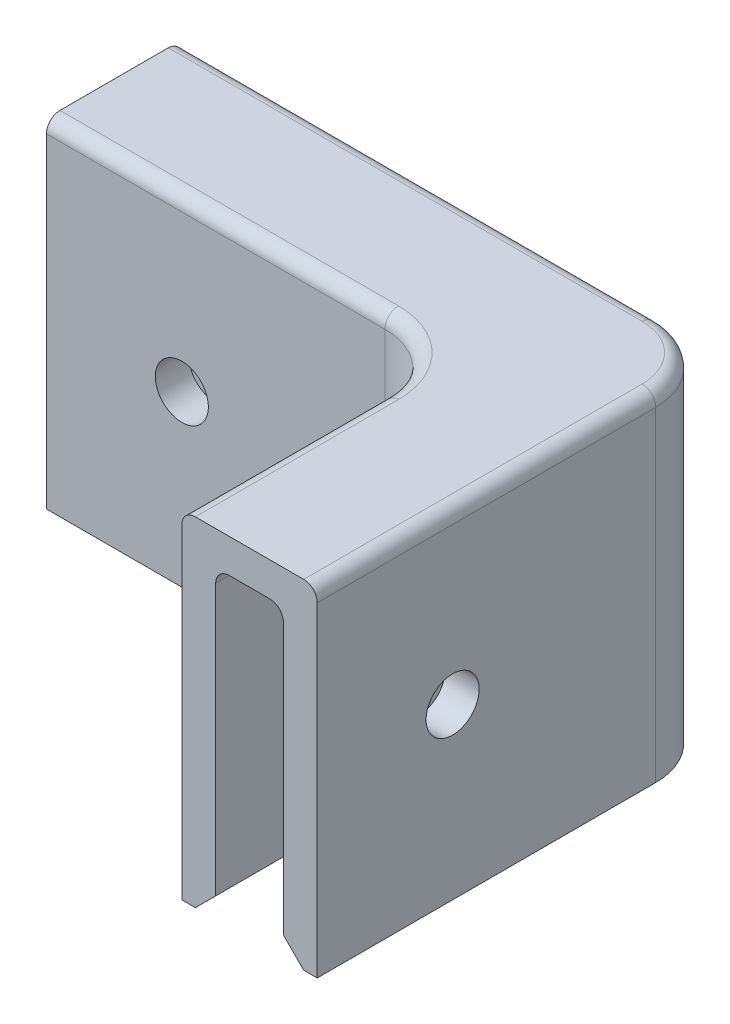
SolidWorks part; units mm, degrees
material "TPU"
ref_plane "Front Plane" through (0, 0, 0) normal (0, 0, 1) x (1, 0, 0)
ref_plane "Top Plane" through (0, 0, 0) normal (0, 1, 0) x (1, 0, 0)
ref_plane "Right Plane" through (0, 0, 0) normal (1, 0, 0) x (0, 0, -1)
sketch "Sketch1" plane through (0, 0, 0) normal (0, 1, 0) x (1, 0, 0)
  line L0 (0, 0) -> (0, -38.1)
  line L1 (0, -38.1) -> (-12.7, -38.1)
  line L2 (-12.7, -38.1) -> (-12.7, -12.7)
  line L3 (-12.7, -12.7) -> (-50.8, -12.7)
  line L4 (-50.8, -12.7) -> (-50.8, 0)
  line L5 (-50.8, 0) -> (0, 0)
  dimension "D1" = 38.1
  dimension "D2" = 50.8
  dimension "D3" = 12.7
extrude "Boss-Extrude1" add sketch "Sketch1" along normal blind 31.75
fillet "Fillet1" radius 6.35 2 edges at (0, 15.875, 0) (-12.7, 15.875, 12.7)
shell "Shell1" thickness 3.175
sketch "Sketch3" plane through (-12.7, 0, 0) normal (-1, 0, 0) x (0, 0, 1)
  line L0 (38.1, 31.75) -> (38.1, 0) construction
  point P0 (25.4, 15.875)
  point P5 (38.1, 15.875)
  dimension "D1" = 12.7
sketch "Sketch4" plane through (0, 0, 12.7) normal (0, 0, 1) x (1, 0, 0)
  line L0 (-50.8, 31.75) -> (-50.8, 0) construction
  point P0 (-38.1, 15.875)
  point P3 (-50.8, 15.875)
  dimension "D1" = 12.7
hole_wizard "#9 (0.196) Diameter Hole1" positions "Sketch3" profile "Sketch5" hole size "#9" standard "ANSI Inch" end condition through all
sketch "Sketch5" plane through (-12.7, 15.875, 25.4) normal (0, 1, 0) x (0, 0, 1)
  line L0 (0, 0) -> (0, 12.7)
  line L1 (0, 12.7) -> (2.4892, 12.7)
  line L2 (2.4892, 12.7) -> (2.4892, 0)
  line L5 (2.4892, 0) -> (0, 0)
  line L11 (0, -6.35) -> (0, 107.95) construction
  dimension "Thru Hole Dia." = 4.9784
  dimension "Thru Hole Depth" = 12.7
hole_wizard "#9 (0.196) Diameter Hole2" positions "Sketch4" profile "Sketch6" hole size "#9" standard "ANSI Inch" end condition through all
sketch "Sketch6" plane through (-38.1, 15.875, 12.7) normal (1, 0, 0) x (0, -1, 0)
  line L0 (0, 0) -> (0, 12.7)
  line L1 (0, 12.7) -> (2.4892, 12.7)
  line L2 (2.4892, 12.7) -> (2.4892, 0)
  line L5 (2.4892, 0) -> (0, 0)
  line L11 (0, -6.35) -> (0, 107.95) construction
  dimension "Thru Hole Dia." = 4.9784
  dimension "Thru Hole Depth" = 12.7
chamfer "Chamfer1" distance 1.905 angle 45 6 edges at (-28.575, 0, 3.175) (-4.1049, 0, 4.1049) (-3.175, 0, 22.225) (-34.925, 0, 9.525) (-12.3148, 0, 12.3148) (-9.525, 0, 28.575)
fillet "Fillet2" radius 1.27 12 edges at (-28.575, 31.75, 0) (-1.8599, 31.75, 1.8599) (-34.925, 31.75, 12.7) (-14.5599, 31.75, 14.5599) (-28.575, 28.575, 3.175) (-4.1049, 28.575, 4.1049) (-34.925, 28.575, 9.525) (-12.3148, 28.575, 12.3148) (0, 31.75, 22.225) (-12.7, 31.75, 28.575) (-3.175, 28.575, 22.225) (-9.525, 28.575, 28.575)
